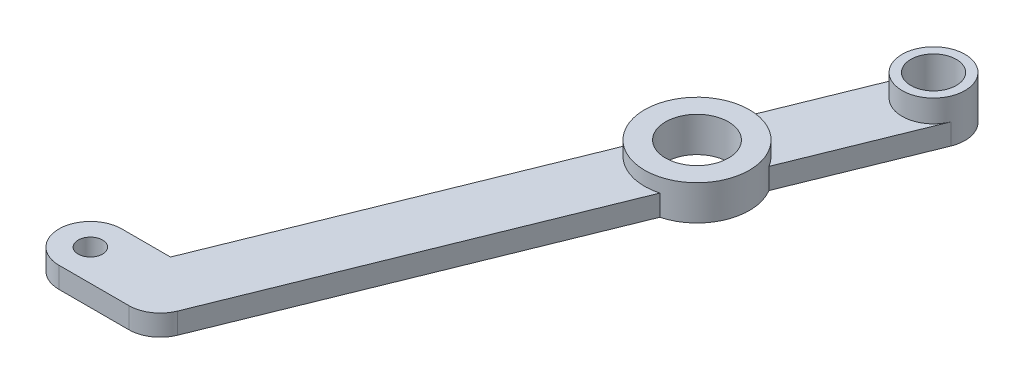
SolidWorks part; units mm, degrees
ref_plane "Front Plane" through (0, 0, 0) normal (0, 0, 1) x (1, 0, 0)
ref_plane "Top Plane" through (0, 0, 0) normal (0, 1, 0) x (1, 0, 0)
ref_plane "Right Plane" through (0, 0, 0) normal (1, 0, 0) x (0, 0, -1)
sketch "Sketch1" plane through (0, 0, 0) normal (0, 1, 0) x (1, 0, 0)
  line L0 (0, 4.5) -> (10, 4.5)
  line L1 (10, 4.5) -> (10, -4.5)
  line L2 (10, -4.5) -> (0, -4.5)
  line L3 (0, -4.5) -> (0, 4.5)
  circle A0 centre (0, 0) radius 4.5
  circle A1 centre (10, 0) radius 4.5
  circle A2 centre (0, 0) radius 1.75
  dimension "D1" = 9
  dimension "D2" = 9
  dimension "D4" = 3.5
  dimension "D3" = 10
extrude "Boss-Extrude1" add sketch "Sketch1" along normal blind 3
sketch "Sketch2" plane through (0, 3, 0) normal (0, 1, 0) x (1, 0, 0)
  line L0 (41.8932, 78.7897) -> (10, 0)
  line L1 (10, 0) -> (14.1712, -1.6885)
  line L2 (14.1712, -1.6885) -> (46.0645, 77.1013)
  line L3 (46.0645, 77.1013) -> (37.722, 80.4782)
  line L4 (37.722, 80.4782) -> (6.9669, 4.5)
  line L5 (0, 4.5) -> (10, 4.5) construction
  circle A0 centre (41.8932, 78.7897) radius 4.5
  arc A1 (10, -4.5) -> (10, 4.5) centre (10, 0) ccw construction
  circle A2 centre (0, 0) radius 1.75 construction
  arc A3 (6.9669, 4.5) -> (14.1712, -1.6885) centre (11.6118, 2.6198) ccw
  arc M4 (10, -4.5) -> (10, 4.5) centre (10, 0) ccw
  line M5 (10, 4.5) -> (0, 4.5)
  dimension "D1" = 9
  dimension "D2" = 62
  dimension "D3" = 85
extrude "Boss-Extrude2" add sketch "Sketch2" against normal blind 3 contours A3 L1 L0 M5 M4 | A0 L0 L2 M4 | L0 L1 M4 | A0 L4 L0 M5 M4 | L3 A0 | L0 A0 L3 | L3 A0 L0
sketch "Sketch3" plane through (0, 3, 0) normal (0, 1, 0) x (1, 0, 0)
  circle A0 centre (41.8932, 78.7897) radius 4.5
  circle A1 centre (41.8932, 78.7897) radius 3.25
  dimension "D1" = 6.5
extrude "Boss-Extrude3" add sketch "Sketch3" along normal blind 3.2
sketch "Sketch4" plane through (0, 3, 0) normal (0, 1, 0) x (1, 0, 0)
  circle A0 centre (41.8932, 78.7897) radius 3.25
extrude "Cut-Extrude1" cut sketch "Sketch4" against normal blind 3
sketch "Sketch6" plane through (0, 0, 0) normal (0, -1, 0) x (1, 0, 0)
  line L0 (14.1712, 1.6885) -> (46.0645, -77.1013) construction
  circle A0 centre (32.1377, -54.6893) radius 7.5
  circle A1 centre (41.8932, -78.7897) radius 3.25 construction
  dimension "D1" = 15
  dimension "D2" = 26
  dimension "D3" = 4.5
extrude "Boss-Extrude4" add sketch "Sketch6" against normal blind 3
sketch "Sketch5" plane through (0, 0, 0) normal (0, -1, 0) x (1, 0, 0)
  line L1 (37.722, -80.4782) -> (30.2177, -61.9394) construction
  circle A0 centre (32.1377, -54.6893) radius 4.5
  circle A1 centre (41.8932, -78.7897) radius 3.25 construction
  dimension "D1" = 9
  dimension "D2" = 26
  dimension "D3" = 4.5
extrude "Cut-Extrude2" cut sketch "Sketch5" against normal through all
sketch "Sketch7" plane through (0, 3, 0) normal (0, 1, 0) x (1, 0, 0)
  circle A0 centre (32.1377, 54.6893) radius 7.5
  circle A1 centre (32.1377, 54.6893) radius 4.5
extrude "Boss-Extrude5" add sketch "Sketch7" along normal blind 2
equation "\"D2@Sketch1\"=\"D1@Sketch1\""
